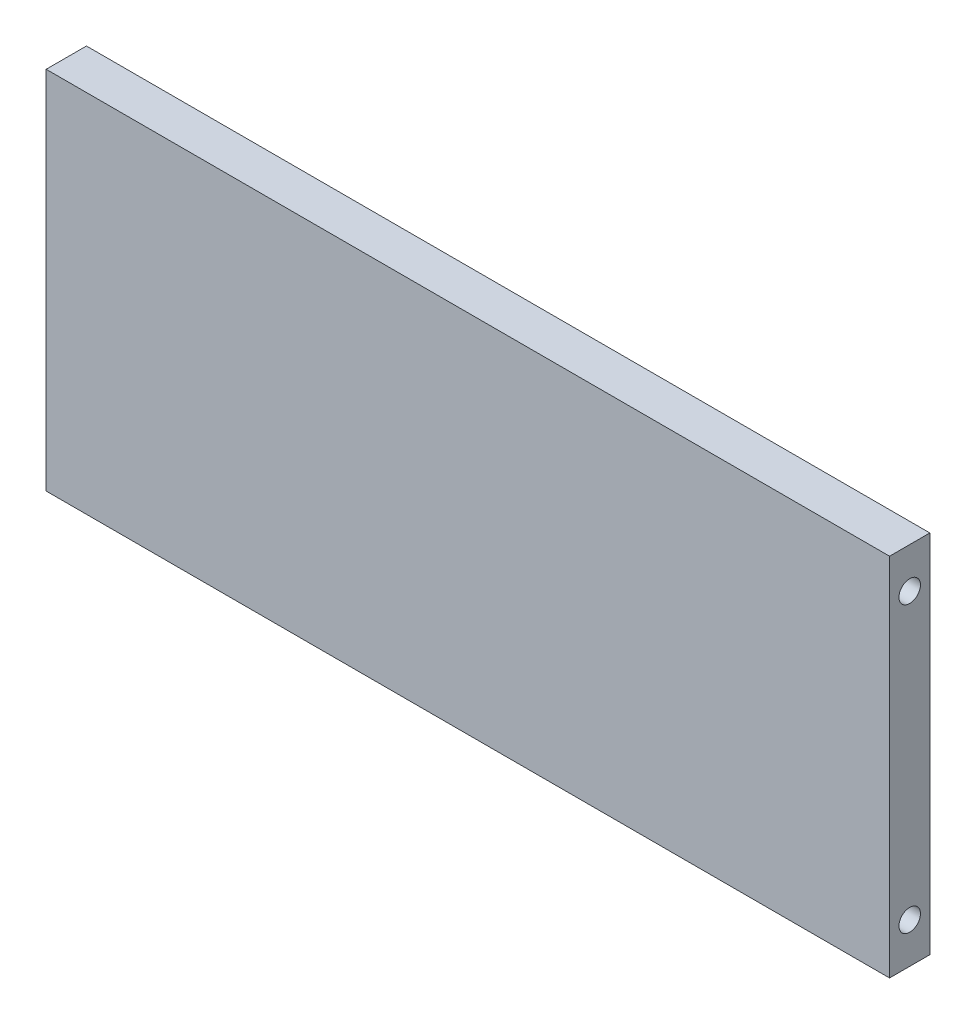
SolidWorks part; units mm, degrees
material "Oak"
ref_plane "Front Plane" through (0, 0, 0) normal (0, 0, 1) x (1, 0, 0)
ref_plane "Top Plane" through (0, 0, 0) normal (0, 1, 0) x (1, 0, 0)
ref_plane "Right Plane" through (0, 0, 0) normal (1, 0, 0) x (0, 0, -1)
sketch "Sketch1" plane through (0, 0, 0) normal (0, 0, 1) x (1, 0, 0)
  line L1 (-157, -68) -> (157, -68)
  line L2 (-157, -68) -> (-157, 68)
  line L3 (-157, 68) -> (157, 68)
  line L4 (157, -68) -> (157, 68)
  line L5 (-157, -68) -> (157, 68) construction
  line L6 (-157, 68) -> (157, -68) construction
  point P0 (0, 0)
  dimension "D1" = 314
  dimension "D2" = 136
extrude "Boss-Extrude1" add sketch "Sketch1" along normal blind 15
sketch "Sketch2" plane through (-157, 0, 0) normal (-1, 0, 0) x (0, 0, 1)
  line L0 (7.5, 68) -> (7.5, 57) construction
  line L3 (15, 68) -> (0, 68) construction
  line L4 (0, -53) -> (15, -53) construction
  line L5 (0, 68) -> (0, -68) construction
  line L6 (15, 68) -> (15, -68) construction
  line L7 (15, -68) -> (0, -68) construction
  circle A1 centre (7.5, 53) radius 4
  dimension "D1" = 8
  dimension "D2" = 11
  dimension "D3" = 15
extrude "Cut-Extrude1" cut sketch "Sketch2" against normal blind 10
pattern_linear "LPattern2" count 2 spacing 106 along (0, -1, 0) of "Cut-Extrude1"
mirror "Mirror1" about plane through (0, 0, 0) normal (1, 0, 0) of "LPattern2", "Cut-Extrude1"
sketch "Sketch3" plane through (0, -68, 0) normal (0, -1, 0) x (1, 0, 0)
  line L0 (142, 15) -> (142, 0) construction
  line L1 (-157, 15) -> (157, 15) construction
  line L2 (-157, 0) -> (157, 0) construction
  line L3 (-157, 7.5) -> (-146, 7.5) construction
  line L4 (-157, 15) -> (-157, 0) construction
  line L5 (157, 15) -> (157, 0) construction
  circle A0 centre (-142, 7.5) radius 4
  dimension "D1" = 8
  dimension "D2" = 11
  dimension "D3" = 15
extrude "Cut-Extrude2" cut sketch "Sketch3" against normal blind 10
pattern_linear "LPattern1" count 3 spacing 142 along (1, 0, 0) of "Cut-Extrude2"
equation "\"A\"= 400 - ( 4 * \"C\" ) - ( 2 * 13mm )"
equation "\"B\"= 151 - \"C\""
equation "\"C\"= 15mm"
equation "\"D1@Sketch1\"=\"A\""
equation "\"D2@Sketch1\"=\"B\""
equation "\"D1@Boss-Extrude1\"=\"C\""
